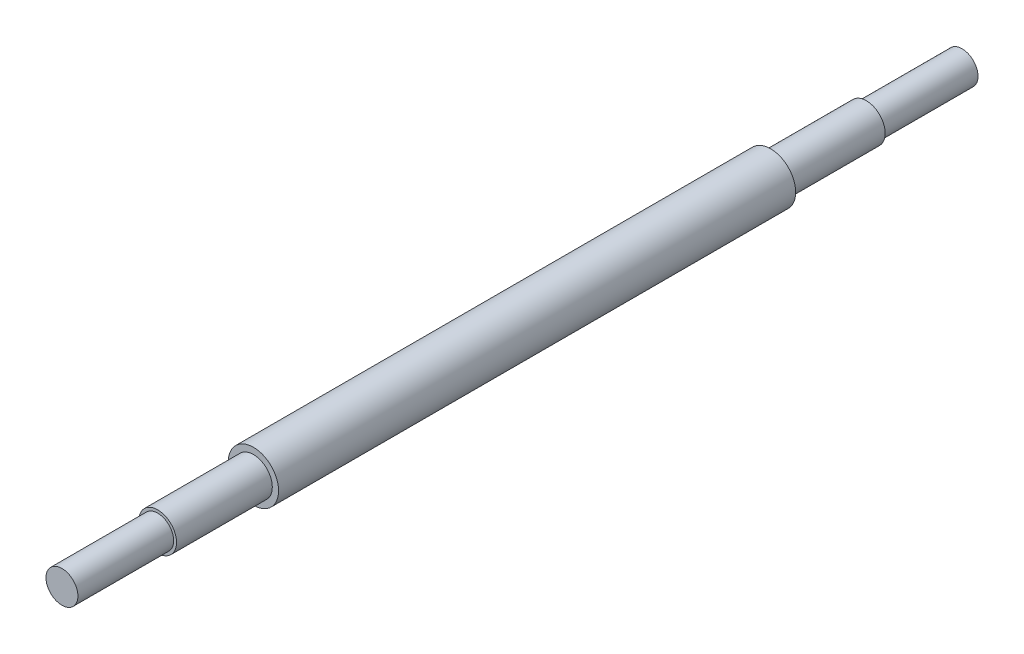
SolidWorks part; units mm, degrees
ref_plane "Front Plane" through (0, 0, 0) normal (0, 0, 1) x (1, 0, 0)
ref_plane "Top Plane" through (0, 0, 0) normal (0, 1, 0) x (1, 0, 0)
ref_plane "Right Plane" through (0, 0, 0) normal (1, 0, 0) x (0, 0, -1)
sketch "Sketch1" plane through (0, 0, 0) normal (0, 0, 1) x (1, 0, 0)
  circle A0 centre (0, 0) radius 20
  dimension "D1" = 40
extrude "Boss-Extrude1" add sketch "Sketch1" against normal blind 411.48 contours A0
sketch "Sketch2" plane through (0, 0, 0) normal (0, 0, 1) x (1, 0, 0)
  circle A0 centre (0, 0) radius 15
  dimension "D1" = 30
extrude "Boss-Extrude2" add sketch "Sketch2" along normal blind 76.2 contours A0
sketch "Sketch3" plane through (0, 0, -411.48) normal (0, 0, -1) x (-1, 0, 0)
  circle A0 centre (0, 0) radius 15
  dimension "D1" = 30
extrude "Boss-Extrude3" add sketch "Sketch3" along normal blind 76.2 contours A0
sketch "Sketch4" plane through (0, 0, 76.2) normal (0, 0, 1) x (1, 0, 0)
  circle A0 centre (0, 0) radius 12.7
  dimension "D1" = 25.4
extrude "Boss-Extrude4" add sketch "Sketch4" along normal blind 76.2
sketch "Sketch5" plane through (0, 0, -487.68) normal (0, 0, -1) x (-1, 0, 0)
  circle A0 centre (0, 0) radius 12.7
  dimension "D1" = 25.4
extrude "Boss-Extrude5" add sketch "Sketch5" along normal blind 76.2
